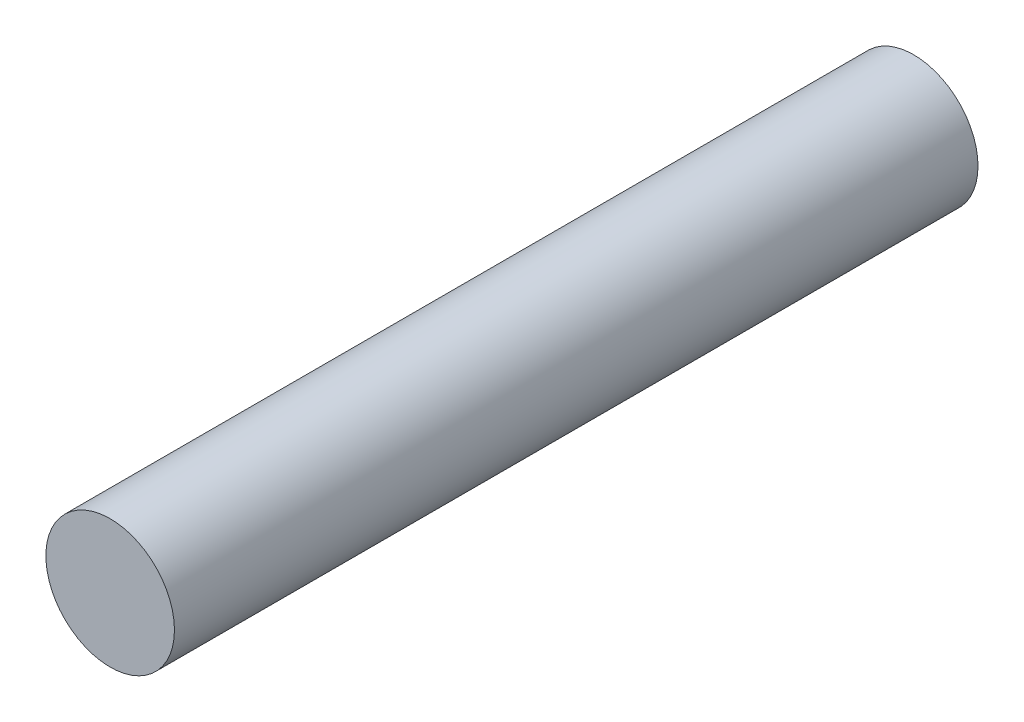
SolidWorks part; units mm, degrees
ref_plane "前视基准面" through (0, 0, 0) normal (0, 0, 1) x (1, 0, 0)
ref_plane "上视基准面" through (0, 0, 0) normal (0, 1, 0) x (1, 0, 0)
ref_plane "右视基准面" through (0, 0, 0) normal (1, 0, 0) x (0, 0, -1)
sketch "草图1" plane through (0, 0, 0) normal (0, 0, 1) x (1, 0, 0)
  circle A0 centre (-11.0871, -4.8584) radius 8
  dimension "D1" = 16
extrude "凸台-拉伸1" add sketch "草图1" along normal blind 100
